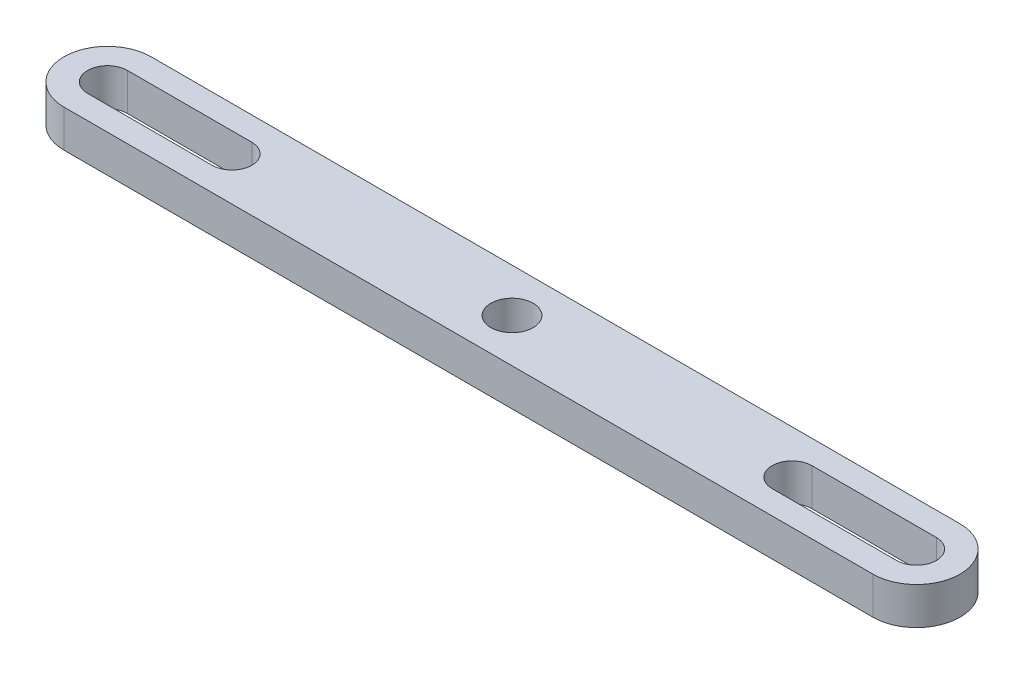
SolidWorks part; units mm, degrees
ref_plane "Спереди" through (0, 0, 0) normal (0, 0, 1) x (1, 0, 0)
ref_plane "Сверху" through (0, 0, 0) normal (0, 1, 0) x (1, 0, 0)
ref_plane "Справа" through (0, 0, 0) normal (1, 0, 0) x (0, 0, -1)
sketch "Эскиз1" plane through (0, 0, 0) normal (0, 1, 0) x (1, 0, 0)
  line L0 (-32.5, 3.5) -> (32.5, 3.5)
  line L1 (-32.5, -3.5) -> (32.5, -3.5)
  line L2 (-32.5, -1.6) -> (-22.5, -1.6)
  line L3 (-32.5, 1.6) -> (-22.5, 1.6)
  line L4 (22.5, 1.6) -> (32.5, 1.6)
  line L5 (22.5, -1.6) -> (32.5, -1.6)
  circle A0 centre (0, 0) radius 1.7
  arc A1 (-22.5, -1.6) -> (-22.5, 1.6) centre (-22.5, 0) ccw
  arc A2 (22.5, 1.6) -> (22.5, -1.6) centre (22.5, 0) ccw
  arc A3 (-32.5, 1.6) -> (-32.5, -1.6) centre (-32.5, 0) ccw
  arc A4 (32.5, -1.6) -> (32.5, 1.6) centre (32.5, 0) ccw
  arc A5 (-32.5, 3.5) -> (-32.5, -3.5) centre (-32.5, 0) ccw
  arc A6 (32.5, -3.5) -> (32.5, 3.5) centre (32.5, 0) ccw
  dimension "D1" = 3.4
  dimension "D2" = 3.2
  dimension "D3" = 3.2
  dimension "D6" = 3.2
  dimension "D7" = 3.2
  dimension "D10" = 7
  dimension "D11" = 7
  dimension "D4" = 22.5
  dimension "D5" = 22.5
  dimension "D8" = 10
  dimension "D9" = 10
extrude "Бобышка-Вытянуть1" add sketch "Эскиз1" along normal blind 3
